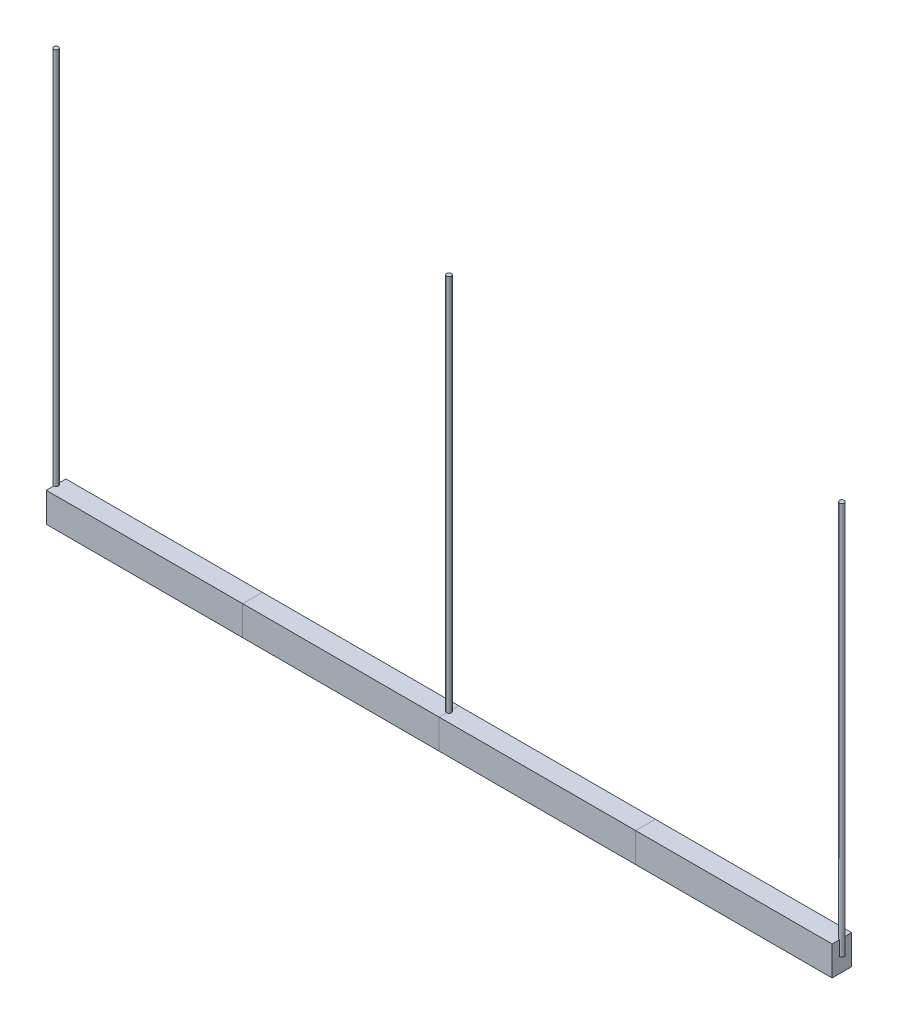
SolidWorks part; units mm, degrees
ref_plane "Front Plane" through (0, 0, 0) normal (0, 0, 1) x (1, 0, 0)
ref_plane "Top Plane" through (0, 0, 0) normal (0, 1, 0) x (1, 0, 0)
ref_plane "Right Plane" through (0, 0, 0) normal (1, 0, 0) x (0, 0, -1)
sketch "Sketch1" plane through (0, 0, 0) normal (1, 0, 0) x (0, 0, -1)
  line L1 (-50, 75) -> (50, 75)
  line L2 (-50, 75) -> (-50, -75)
  line L3 (-50, -75) -> (50, -75)
  line L4 (50, 75) -> (50, -75)
  line L5 (-50, 75) -> (50, -75) construction
  line L6 (-50, -75) -> (50, 75) construction
  point P0 (0, 0)
  dimension "D1" = 150
  dimension "D2" = 100
extrude "Segment 1" add sketch "Sketch1" along normal blind 1000
sketch "Sketch2" plane through (1000, 0, 0) normal (1, 0, 0) x (0, 0, -1)
  line L4 (50, -75) -> (50, 75)
  line L5 (50, 75) -> (-50, 75)
  line L6 (-50, 75) -> (-50, -75)
  line L7 (-50, -75) -> (50, -75)
  line L8 (50, -75) -> (50, 75)
  line L9 (50, 75) -> (-50, 75)
  line L10 (-50, 75) -> (-50, -75)
  line L11 (-50, -75) -> (50, -75)
  dimension "D1" = 0
extrude "Segment 2" add sketch "Sketch2" along normal blind 1000 separate body
sketch "Sketch3" plane through (2000, 0, 0) normal (1, 0, 0) x (0, 0, -1)
  line L4 (-50, -75) -> (50, -75)
  line L5 (50, -75) -> (50, 75)
  line L6 (50, 75) -> (-50, 75)
  line L7 (-50, 75) -> (-50, -75)
  line L8 (-50, -75) -> (50, -75)
  line L9 (50, -75) -> (50, 75)
  line L10 (50, 75) -> (-50, 75)
  line L11 (-50, 75) -> (-50, -75)
  dimension "D1" = 0
extrude "Segment 3" add sketch "Sketch3" along normal blind 1000 separate body
sketch "Sketch4" plane through (3000, 0, 0) normal (1, 0, 0) x (0, 0, -1)
  line L4 (-50, 75) -> (-50, -75)
  line L5 (-50, -75) -> (50, -75)
  line L6 (50, -75) -> (50, 75)
  line L7 (50, 75) -> (-50, 75)
  line L8 (-50, 75) -> (-50, -75)
  line L9 (-50, -75) -> (50, -75)
  line L10 (50, -75) -> (50, 75)
  line L11 (50, 75) -> (-50, 75)
  dimension "D1" = 0
extrude "Segment 4" add sketch "Sketch4" along normal blind 1000 separate body
sketch "Sketch5" plane through (0, 0, 0) normal (0, 1, 0) x (1, 0, 0)
  line L0 (2000, 50) -> (2000, -50) construction
  line L1 (4000, 50) -> (4000, -50) construction
  circle A0 centre (0, 0) radius 12
  circle A1 centre (2000, 0) radius 12
  circle A2 centre (4000, 0) radius 12
  dimension "D1" = 24
extrude "Linkages" add sketch "Sketch5" along normal blind 2000 separate body
